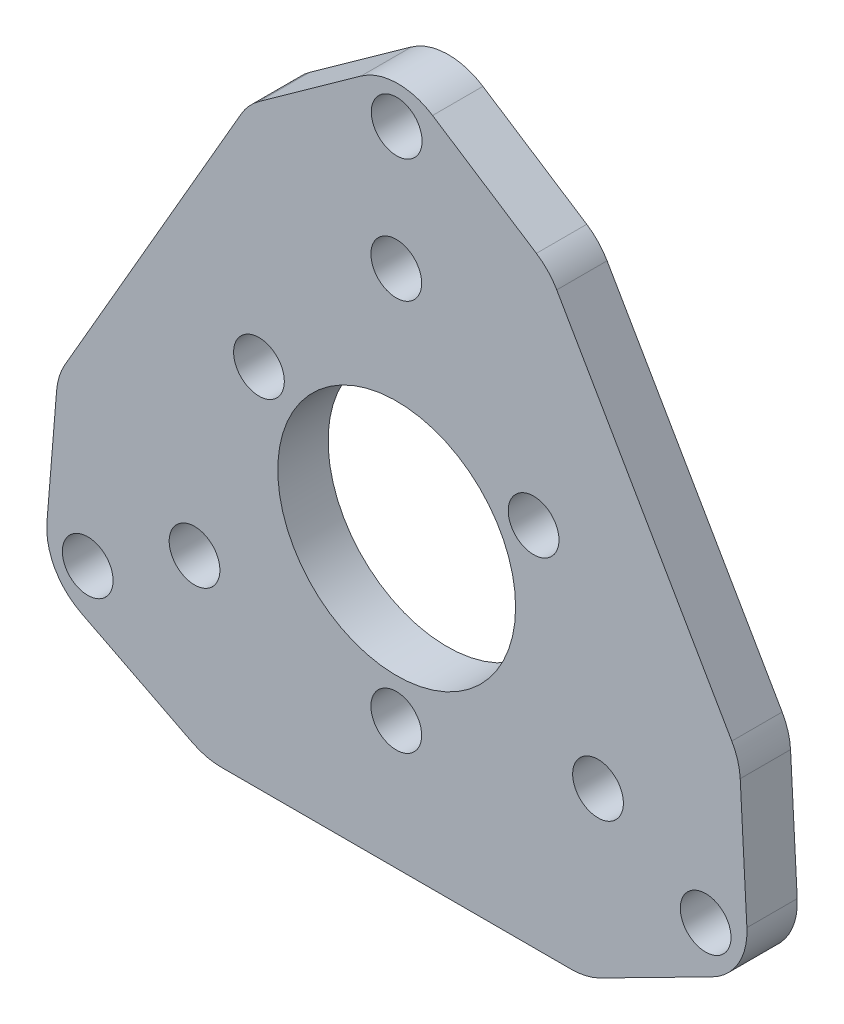
SolidWorks part; units mm, degrees
material "Acrylic (Medium-high impact)"
ref_plane "Front" through (0, 0, 0) normal (0, 0, 1) x (1, 0, 0)
ref_plane "Top" through (0, 0, 0) normal (0, 1, 0) x (1, 0, 0)
ref_plane "Right" through (0, 0, 0) normal (1, 0, 0) x (0, 0, -1)
sketch "Sketch1" plane through (0, 0, 0) normal (0, 0, 1) x (1, 0, 0)
  line L0 (31.8906, 32.2685) -> (22.25, 38.5381) construction
  line L1 (43.8906, 11.4838) -> (31.8906, 32.2685) construction
  line L2 (44.5, 0) -> (43.8906, 11.4838) construction
  line L3 (34.25, -5.2142) -> (44.5, 0) construction
  line L4 (10.25, -5.2142) -> (34.25, -5.2142) construction
  line L5 (0, 0) -> (10.25, -5.2142) construction
  line L6 (0.8998, 11.0585) -> (0, 0) construction
  line L7 (0.8998, 11.0585) -> (12.8998, 31.8431) construction
  line L8 (12.8998, 31.8431) -> (22.25, 38.5381) construction
  line L9 (31.0867, 32.7912) -> (24.5392, 37.0494)
  line L10 (43.4111, 12.3143) -> (32.3701, 31.438)
  line L11 (44.3621, 2.5977) -> (43.9414, 10.5263)
  line L12 (35.1047, -4.7794) -> (42.1814, -1.1795)
  line L13 (11.2089, -5.2142) -> (33.2911, -5.2142)
  line L14 (2.3907, -1.2162) -> (9.3953, -4.7794)
  line L15 (0.8268, 10.1619) -> (0.2175, 2.6734)
  line L16 (1.3496, 11.8375) -> (12.4674, 31.0942)
  line L17 (13.6028, 32.3465) -> (20.0297, 36.9484)
  line L18 (41.9378, 9.5622) -> (34.9378, -2.5622) construction
  line L19 (42.3708, 9.3122) -> (35.3708, -2.8122)
  line L20 (41.5048, 9.8122) -> (34.5048, -2.3122)
  line L21 (33.8665, 12.846) -> (28.0583, 22.9063) construction
  line L22 (28.0583, 2.7858) -> (33.8665, 12.846) construction
  line L23 (16.4417, 2.7858) -> (28.0583, 2.7858) construction
  line L24 (10.6335, 12.846) -> (16.4417, 2.7858) construction
  line L25 (16.4417, 22.9063) -> (10.6335, 12.846) construction
  line L26 (28.0583, 22.9063) -> (16.4417, 22.9063) construction
  line L27 (33.8665, 12.846) -> (28.0583, 22.9063) construction
  line L28 (28.0583, 2.7858) -> (33.8665, 12.846) construction
  line L29 (16.4417, 2.7858) -> (28.0583, 2.7858) construction
  line L30 (10.6335, 12.846) -> (16.4417, 2.7858) construction
  line L31 (16.4417, 22.9063) -> (10.6335, 12.846) construction
  line L32 (28.0583, 22.9063) -> (16.4417, 22.9063) construction
  line L33 (22.25, 12.846) -> (44.5, 0) construction
  line L34 (22.25, 12.846) -> (7.0114, 21.6441) construction
  line L37 (10.0175, -2.3499) -> (3.0175, 9.7744)
  line L40 (9.1515, -2.8499) -> (2.1515, 9.2744)
  line L41 (9.5845, -2.5999) -> (2.5845, 9.5244) construction
  line L42 (15.3585, 31.0381) -> (29.3585, 31.0381)
  line L43 (15.3585, 32.0381) -> (29.3585, 32.0381)
  line L44 (15.3585, 31.5381) -> (29.3585, 31.5381) construction
  line L45 (9.5263, 5.5) -> (4.2044, 2.3491) construction
  arc A1 (9.1515, -2.8499) -> (10.0175, -2.3499) centre (9.5845, -2.5999) ccw
  arc A3 (3.0175, 9.7744) -> (2.1515, 9.2744) centre (2.5845, 9.5244) ccw
  arc A4 (15.3585, 32.0381) -> (15.3585, 31.0381) centre (15.3585, 31.5381) ccw
  arc A12 (31.0867, 32.7912) -> (32.3701, 31.438) centre (28.906, 29.438) cw
  arc A13 (43.4111, 12.3143) -> (43.9414, 10.5263) centre (39.947, 10.3143) cw
  arc A14 (44.3621, 2.5977) -> (42.1814, -1.1795) centre (40.3678, 2.3857) cw
  arc A15 (35.1047, -4.7794) -> (33.2911, -5.2142) centre (33.2911, -1.2142) cw
  arc A16 (11.2089, -5.2142) -> (9.3953, -4.7794) centre (11.2089, -1.2142) cw
  arc A17 (2.3907, -1.2162) -> (0.2175, 2.6734) centre (4.2044, 2.3491) cw
  arc A18 (0.8268, 10.1619) -> (1.3496, 11.8375) centre (4.8137, 9.8375) cw
  arc A19 (12.4674, 31.0942) -> (13.6028, 32.3465) centre (15.9315, 29.0942) cw
  arc A20 (24.5392, 37.0494) -> (20.0297, 36.9484) centre (22.3585, 33.6961) ccw
  arc A21 (42.3708, 9.3122) -> (41.5048, 9.8122) centre (41.9378, 9.5622) ccw
  arc A22 (34.5048, -2.3122) -> (35.3708, -2.8122) centre (34.9378, -2.5622) ccw
  circle A23 centre (22.25, 12.846) radius 10.0602 construction
  circle A24 centre (9.5263, 5.5) radius 1.6 construction
  circle A29 centre (34.9737, 5.5) radius 1.6 construction
  circle A31 centre (22.25, 27.5381) radius 1.6 construction
  circle A32 centre (13.5897, 17.846) radius 1.6
  circle A33 centre (9.5263, 5.5) radius 1.6
  circle A34 centre (34.9737, 5.5) radius 1.6
  circle A35 centre (30.9103, 17.846) radius 1.6
  circle A36 centre (22.25, 27.5381) radius 1.6
  circle A38 centre (22.25, 2.846) radius 1.6
  arc A39 (29.3585, 31.0381) -> (29.3585, 32.0381) centre (29.3585, 31.5381) ccw
  circle A40 centre (22.25, 12.846) radius 10 construction
  point P56 (38.4378, 3.5)
  point P76 (6.0845, 3.4622)
  point P85 (22.3585, 31.5381)
  dimension "D1" = 4
  dimension "D3" = 20
  dimension "D2" = 14
  dimension "D4" = 4
  dimension "D5" = 1
extrude "Boss-Extrude1" add sketch "Sketch1" along normal blind 3.175
sketch "Sketch2" plane through (0, 0, 3.175) normal (0, 0, 1) x (1, 0, 0)
  circle A0 centre (22.2755, 12.8138) radius 24.8824 construction
  circle A1 centre (41.761, 1.5638) radius 1.6
  arc A2 (24.5392, 37.0494) -> (20.0297, 36.9484) centre (22.3585, 33.6961) ccw construction
  arc A3 (42.1814, -1.1795) -> (44.3621, 2.5977) centre (40.3678, 2.3857) ccw construction
  circle A4 centre (2.7899, 1.5638) radius 1.6
  arc A6 (0.2175, 2.6734) -> (2.3907, -1.2162) centre (4.2044, 2.3491) ccw construction
  circle A7 centre (22.2755, 12.8138) radius 7.5
  circle A8 centre (22.2755, 35.3138) radius 1.6
  circle A9 centre (22.25, 27.5381) radius 1.6 construction
  dimension "D1" = 15
  dimension "D2" = 22.5
  dimension "D3" = 3
extrude "Cut-Extrude1" cut sketch "Sketch2" against normal through all
sketch "Sketch3" plane through (0, 0, 3.175) normal (0, 0, 1) x (1, 0, 0)
  line L0 (42.3708, 9.3122) -> (35.3708, -2.8122) construction
  line L1 (41.5048, 9.8122) -> (34.5048, -2.3122) construction
  line L2 (10.0175, -2.3499) -> (3.0175, 9.7744) construction
  line L3 (9.1515, -2.8499) -> (2.1515, 9.2744) construction
  line L4 (15.3585, 31.0381) -> (29.3585, 31.0381) construction
  line L5 (15.3585, 32.0381) -> (29.3585, 32.0381) construction
  line L6 (42.3708, 9.3122) -> (35.3708, -2.8122)
  line L7 (41.5048, 9.8122) -> (34.5048, -2.3122)
  line L8 (10.0175, -2.3499) -> (3.0175, 9.7744)
  line L9 (9.1515, -2.8499) -> (2.1515, 9.2744)
  line L10 (15.3585, 31.0381) -> (29.3585, 31.0381)
  line L11 (15.3585, 32.0381) -> (29.3585, 32.0381)
  arc A0 (42.3708, 9.3122) -> (41.5048, 9.8122) centre (41.9378, 9.5622) ccw construction
  arc A1 (34.5048, -2.3122) -> (35.3708, -2.8122) centre (34.9378, -2.5622) ccw construction
  arc A2 (9.1515, -2.8499) -> (10.0175, -2.3499) centre (9.5845, -2.5999) ccw construction
  arc A3 (3.0175, 9.7744) -> (2.1515, 9.2744) centre (2.5845, 9.5244) ccw construction
  arc A4 (29.3585, 31.0381) -> (29.3585, 32.0381) centre (29.3585, 31.5381) ccw construction
  arc A5 (15.3585, 32.0381) -> (15.3585, 31.0381) centre (15.3585, 31.5381) ccw construction
  arc A6 (42.3708, 9.3122) -> (41.5048, 9.8122) centre (41.9378, 9.5622) ccw
  arc A7 (34.5048, -2.3122) -> (35.3708, -2.8122) centre (34.9378, -2.5622) ccw
  arc A8 (9.1515, -2.8499) -> (10.0175, -2.3499) centre (9.5845, -2.5999) ccw
  arc A9 (3.0175, 9.7744) -> (2.1515, 9.2744) centre (2.5845, 9.5244) ccw
  arc A10 (29.3585, 31.0381) -> (29.3585, 32.0381) centre (29.3585, 31.5381) ccw
  arc A11 (15.3585, 32.0381) -> (15.3585, 31.0381) centre (15.3585, 31.5381) ccw
extrude "Boss-Extrude3" add sketch "Sketch3" against normal up to surface (3.175 mm away) up to face at (4.3899, 1.5638, 0)
